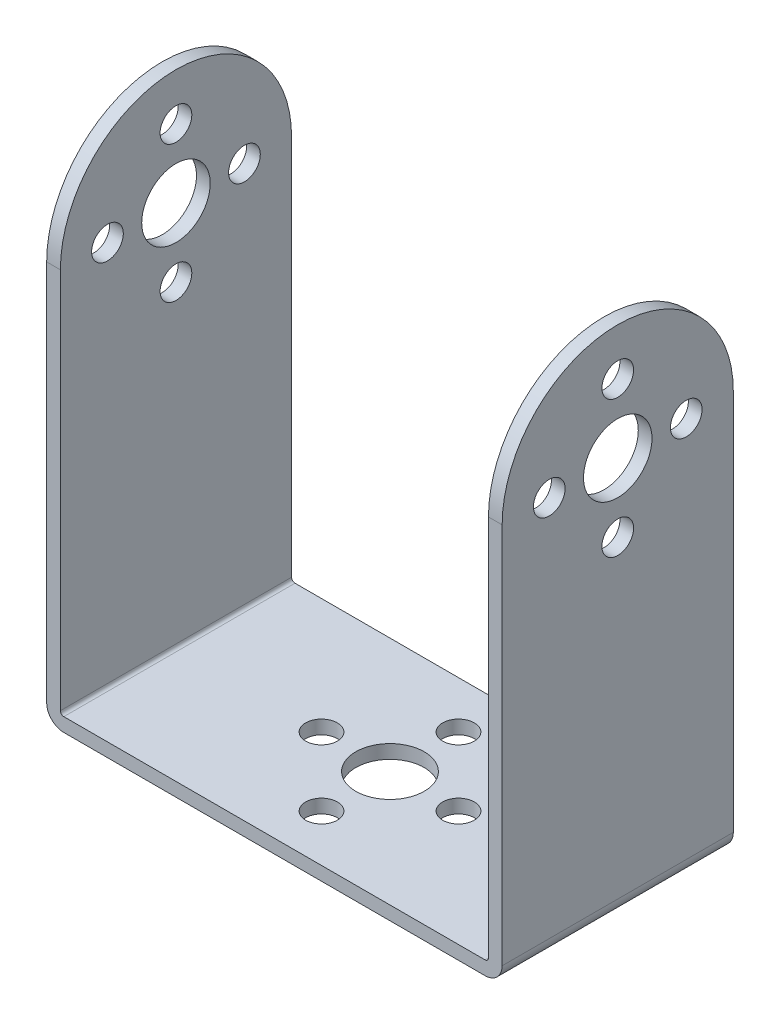
SolidWorks part; units mm, degrees
material "2024 Alloy"
ref_plane "Front Plane" through (0, 0, 0) normal (0, 0, 1) x (1, 0, 0)
ref_plane "Top Plane" through (0, 0, 0) normal (0, 1, 0) x (1, 0, 0)
ref_plane "Right Plane" through (0, 0, 0) normal (1, 0, 0) x (0, 0, -1)
ref_plane "Plane1" through (26.6, 0, 0) normal (1, 0, 0) x (0, 0, -1)
sketch "Sketch1" plane through (26.6, 0, 0) normal (1, 0, 0) x (0, 0, -1)
  line L0 (-13.5, 45) -> (-13.5, -1.6)
  line L1 (-13.5, -1.6) -> (13.5, -1.6)
  line L2 (13.5, -1.6) -> (13.5, 45)
  arc A0 (13.5, 45) -> (-13.5, 45) centre (0, 45) ccw
extrude "Boss-Extrude1" add sketch "Sketch1" against normal blind 53.2
sketch "Sketch2" plane through (0, 0, -13.5) normal (0, 0, -1) x (-1, 0, 0)
  line L0 (-25, 63.5) -> (-25, 0)
  line L1 (-25, 0) -> (25, 0)
  line L2 (25, 0) -> (25, 63.5)
  line L3 (25, 63.5) -> (-25, 63.5)
  dimension "D1" = 50
  dimension "D2" = 63.5
extrude "Cut-Extrude1" cut sketch "Sketch2" against normal through all
hole_wizard "Ø8.0 (8) Diameter Hole1" positions "Sketch4" profile "Sketch3" hole size "Ø8.0" standard "ANSI Metric"
sketch "Sketch4" plane through (-26.6, 0, 0) normal (-1, 0, 0) x (0, 0, 1)
  point P0 (0, 45)
sketch "Sketch3" plane through (-26.6, 45, 0) normal (0, 1, 0) x (0, 0, 1)
  line L0 (0, 0) -> (0, 1.6)
  line L1 (0, 1.6) -> (4, 1.6)
  line L2 (4, 1.6) -> (4, 0)
  line L5 (4, 0) -> (0, 0)
  line L11 (0, -6.35) -> (0, 107.95) construction
  dimension "Thru Hole Dia." = 8
  dimension "Thru Hole Depth" = 1.6
hole_wizard "Ø3.7 (3.7) Diameter Hole1" positions "Sketch6" profile "Sketch5" hole size "Ø3.7" standard "ANSI Metric" end condition through all
sketch "Sketch6" plane through (-26.6, 0, 0) normal (-1, 0, 0) x (0, 0, 1)
  point P0 (0, 53)
  point P1 (-8, 45)
  point P2 (0, 37)
  point P3 (8, 45)
sketch "Sketch5" plane through (-26.6, 53, 0) normal (0, 1, 0) x (0, 0, 1)
  line L0 (0, 0) -> (0, 53.2)
  line L1 (0, 53.2) -> (1.85, 53.2)
  line L2 (1.85, 53.2) -> (1.85, 0)
  line L5 (1.85, 0) -> (0, 0)
  line L11 (0, -6.35) -> (0, 107.95) construction
  dimension "Thru Hole Dia." = 3.7
  dimension "Thru Hole Depth" = 53.2
hole_wizard "Ø3.7 (3.7) Diameter Hole2" positions "Sketch8" profile "Sketch7" hole size "Ø3.7" standard "ANSI Metric"
sketch "Sketch8" plane through (0, 0, 0) normal (0, 1, 0) x (1, 0, 0)
  point P0 (0, 8)
  point P1 (8, 0)
  point P2 (0, -8)
  point P3 (-8, 0)
sketch "Sketch7" plane through (0, 0, -8) normal (1, 0, 0) x (0, 0, 1)
  line L0 (0, 0) -> (0, 1.6)
  line L1 (0, 1.6) -> (1.85, 1.6)
  line L2 (1.85, 1.6) -> (1.85, 0)
  line L5 (1.85, 0) -> (0, 0)
  line L11 (0, -6.35) -> (0, 107.95) construction
  dimension "Thru Hole Dia." = 3.7
  dimension "Thru Hole Depth" = 1.6
hole_wizard "Ø8.0 (8) Diameter Hole2" positions "Sketch10" profile "Sketch9" hole size "Ø8.0" standard "ANSI Metric"
sketch "Sketch10" plane through (0, 0, 0) normal (0, 1, 0) x (1, 0, 0)
  point P0 (0, 0)
sketch "Sketch9" plane through (0, 0, 0) normal (1, 0, 0) x (0, 0, 1)
  line L0 (0, 0) -> (0, 1.6)
  line L1 (0, 1.6) -> (4, 1.6)
  line L2 (4, 1.6) -> (4, 0)
  line L5 (4, 0) -> (0, 0)
  line L11 (0, -6.35) -> (0, 107.95) construction
  dimension "Thru Hole Dia." = 8
  dimension "Thru Hole Depth" = 1.6
hole_wizard "Ø8.0 (8) Diameter Hole3" positions "Sketch12" profile "Sketch11" hole size "Ø8.0" standard "ANSI Metric"
sketch "Sketch12" plane through (26.6, 0, 0) normal (1, 0, 0) x (0, 0, -1)
  point P0 (0, 45)
sketch "Sketch11" plane through (26.6, 45, 0) normal (0, 1, 0) x (0, 0, -1)
  line L0 (0, 0) -> (0, 1.6)
  line L1 (0, 1.6) -> (4, 1.6)
  line L2 (4, 1.6) -> (4, 0)
  line L5 (4, 0) -> (0, 0)
  line L11 (0, -6.35) -> (0, 107.95) construction
  dimension "Thru Hole Dia." = 8
  dimension "Thru Hole Depth" = 1.6
fillet "Fillet1" radius 0.4 2 edges at (25, 0, 0) (-25, 0, 0)
fillet "Fillet2" radius 2 2 edges at (-26.6, -1.6, 0) (26.6, -1.6, 0)
